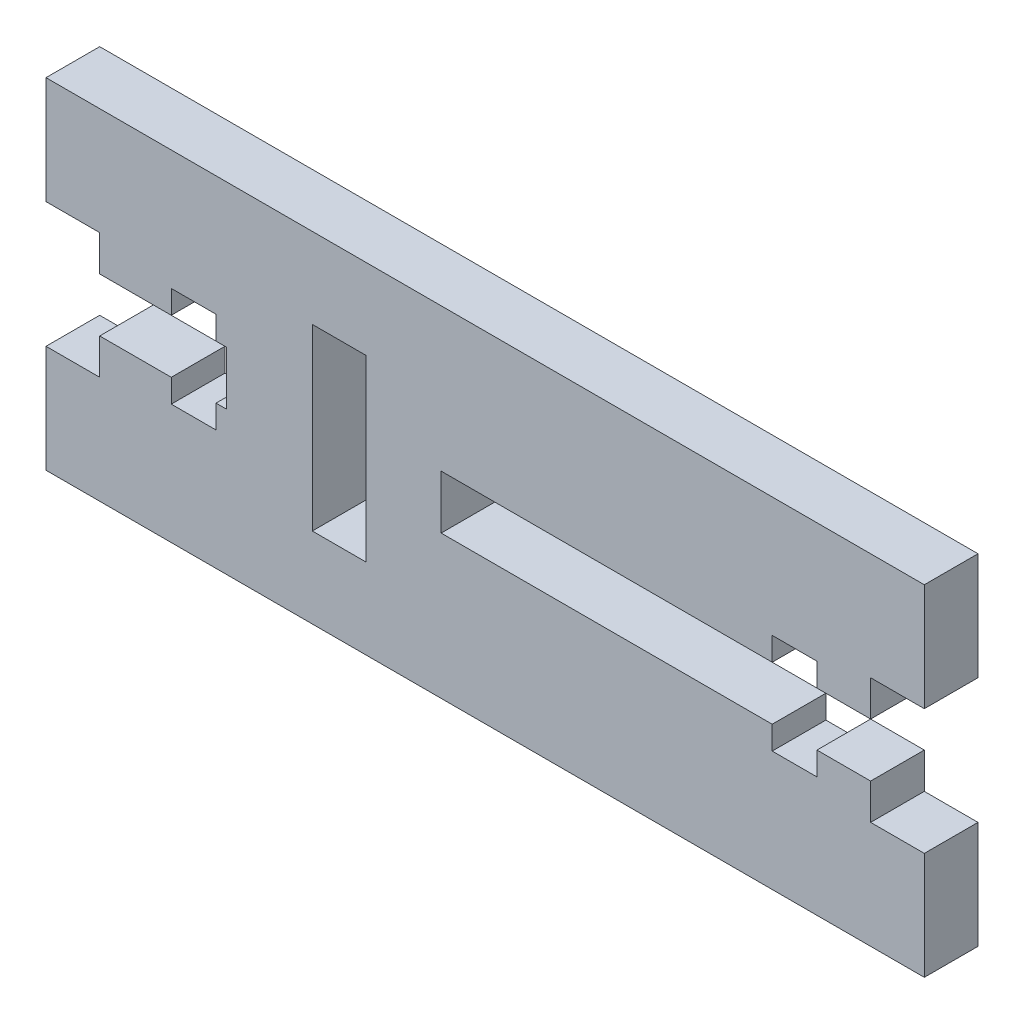
SolidWorks part; units mm, degrees
ref_plane "Front Plane" through (0, 0, 0) normal (0, 0, 1) x (1, 0, 0)
ref_plane "Top Plane" through (0, 0, 0) normal (0, 1, 0) x (1, 0, 0)
ref_plane "Right Plane" through (0, 0, 0) normal (1, 0, 0) x (0, 0, -1)
sketch "Model" plane through (0, 0, 0) normal (0, 0, 1) x (1, 0, 0)
  line L0 (73.79, 50.5) -> (24.71, 50.5)
  line L2 (46.51, 31.5) -> (24.71, 31.5)
  line L3 (39.59, 36.0001) -> (39.59, 46)
  line L4 (42.59, 36.0001) -> (39.59, 36.0001)
  line L5 (42.59, 46) -> (42.59, 36.0001)
  line L6 (39.59, 46) -> (42.59, 46)
  line L7 (27.71, 37.5) -> (24.71, 37.5)
  line L8 (27.71, 39.5) -> (27.71, 37.5)
  line L9 (31.71, 39.5) -> (27.71, 39.5)
  line L10 (31.71, 38.2) -> (31.71, 39.5)
  line L11 (34.21, 38.2) -> (31.71, 38.2)
  line L12 (34.21, 39.5) -> (34.21, 38.2)
  line L13 (34.81, 39.5) -> (34.21, 39.5)
  line L14 (34.81, 42.5) -> (34.81, 39.5)
  line L15 (34.21, 42.5) -> (34.81, 42.5)
  line L16 (34.21, 43.8) -> (34.21, 42.5)
  line L17 (31.71, 43.8) -> (34.21, 43.8)
  line L18 (31.71, 42.5) -> (31.71, 43.8)
  line L19 (27.71, 42.5) -> (31.71, 42.5)
  line L20 (27.71, 44.5) -> (27.71, 42.5)
  line L21 (24.71, 44.5) -> (27.71, 44.5)
  line L22 (70.79, 44.5) -> (73.79, 44.5)
  line L23 (70.79, 42.5) -> (70.79, 44.5)
  line L24 (67.79, 42.5) -> (70.79, 42.5)
  line L25 (67.79, 43.8) -> (67.79, 42.5)
  line L26 (65.29, 43.8) -> (67.79, 43.8)
  line L27 (65.29, 42.5) -> (65.29, 43.8)
  line L28 (46.79, 42.5) -> (65.29, 42.5)
  line L29 (46.79, 39.5) -> (46.79, 42.5)
  line L30 (65.29, 39.5) -> (46.79, 39.5)
  line L31 (65.29, 38.2) -> (65.29, 39.5)
  line L32 (67.79, 38.2) -> (65.29, 38.2)
  line L33 (67.79, 39.5) -> (67.79, 38.2)
  line L34 (70.79, 39.5) -> (67.79, 39.5)
  line L35 (70.79, 37.5) -> (70.79, 39.5)
  line L36 (73.79, 37.5) -> (70.79, 37.5)
  line L37 (73.79, 31.5) -> (73.79, 37.5)
  line L38 (46.51, 31.5) -> (73.79, 31.5)
  line L39 (24.71, 50.5) -> (24.71, 44.5)
  line L40 (24.71, 37.5) -> (24.71, 31.5)
  line L41 (73.79, 44.5) -> (73.79, 50.5)
  dimension "D2" = 3
  dimension "D4" = 3
  dimension "D5" = 4
  dimension "D6" = 2.5
  dimension "D7" = 0.6
extrude "Boss-Extrude1" add sketch "Model" along normal blind 3
